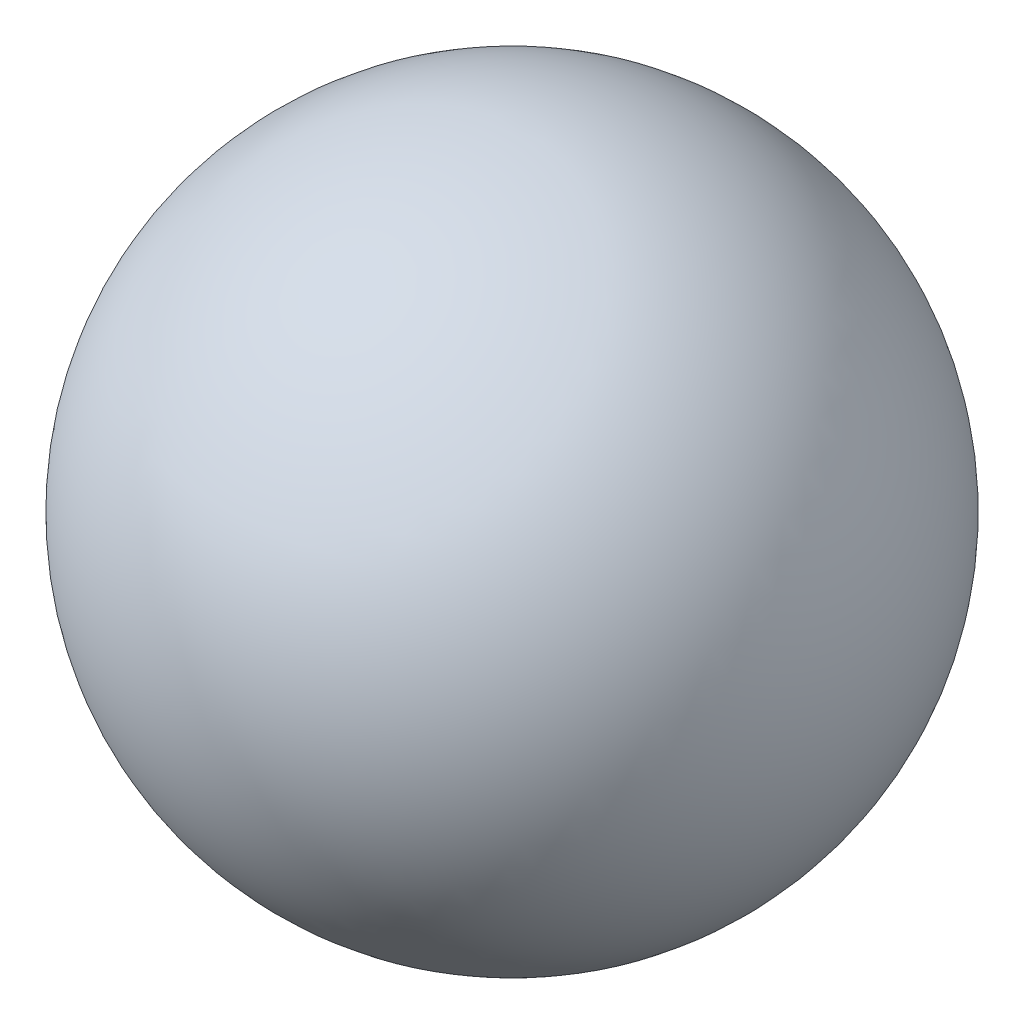
SolidWorks part; units mm, degrees
ref_plane "前视基准面" through (0, 0, 0) normal (0, 0, 1) x (1, 0, 0)
ref_plane "上视基准面" through (0, 0, 0) normal (0, 1, 0) x (1, 0, 0)
ref_plane "右视基准面" through (0, 0, 0) normal (1, 0, 0) x (0, 0, -1)
sketch "草图1" plane through (0, 0, 0) normal (0, 0, 1) x (1, 0, 0)
  line L0 (0, 34) -> (0, -34)
  arc A0 (0, -34) -> (0, 34) centre (0, 0) cw
  dimension "D1" = 34
  dimension "D2" = 68
revolve "旋转1" add sketch "草图1" angle 360 about L0
